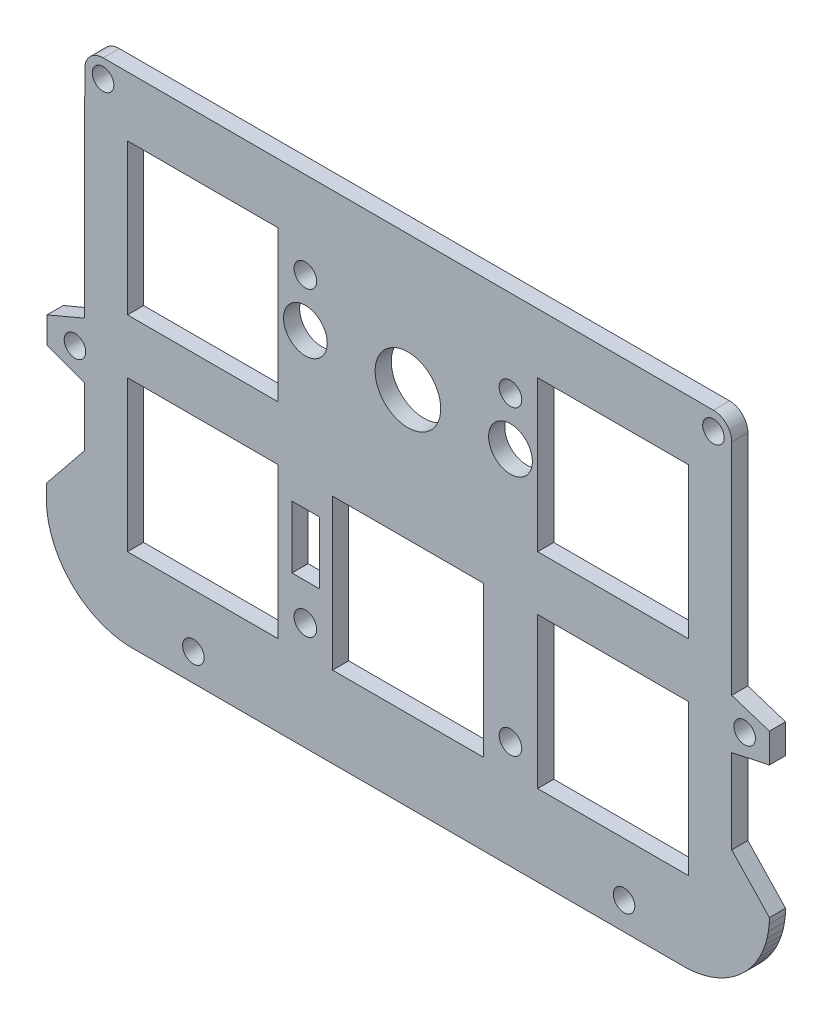
SolidWorks part; units mm, degrees
ref_plane "Front Plane" through (0, 0, 0) normal (0, 0, 1) x (1, 0, 0)
ref_plane "Top Plane" through (0, 0, 0) normal (0, 1, 0) x (1, 0, 0)
ref_plane "Right Plane" through (0, 0, 0) normal (1, 0, 0) x (0, 0, -1)
sketch "Model" plane through (0, 0, 0) normal (0, 0, 1) x (1, 0, 0)
  line L0 (16.6205, 16.7817) -> (2.621, 16.7817)
  line L1 (2.621, 16.7817) -> (2.621, 2.7823)
  line L2 (2.621, 2.7823) -> (16.6205, 2.7823)
  line L3 (16.6205, 2.7823) -> (16.6205, 16.7817)
  line L4 (54.7204, 35.8316) -> (40.7211, 35.8316)
  line L5 (40.7211, 35.8316) -> (40.7211, 21.8323)
  line L6 (40.7211, 21.8323) -> (54.7204, 21.8323)
  line L7 (54.7204, 21.8323) -> (54.7204, 35.8316)
  line L8 (21.671, 16.7817) -> (21.671, 2.7823)
  line L9 (21.671, 2.7823) -> (35.6704, 2.7823)
  line L10 (35.6704, 2.7823) -> (35.6704, 16.7817)
  line L11 (35.6704, 16.7817) -> (21.671, 16.7817)
  line L12 (16.6205, 21.8323) -> (16.6205, 35.8316)
  line L13 (16.6205, 35.8316) -> (2.621, 35.8316)
  line L14 (2.621, 35.8316) -> (2.621, 21.8323)
  line L15 (2.621, 21.8323) -> (16.6205, 21.8323)
  line L16 (40.7211, 16.7817) -> (40.7211, 2.7823)
  line L17 (40.7211, 2.7823) -> (54.7204, 2.7823)
  line L18 (54.7204, 2.7823) -> (54.7204, 16.7817)
  line L19 (54.7204, 16.7817) -> (40.7211, 16.7817)
  line L20 (0.3548, 41.3789) -> (57.0464, 41.3789)
  line L21 (62.2453, 3.1661) -> (62.2262, 2.6367)
  line L22 (62.2262, 2.6367) -> (62.1524, 2.0114)
  line L23 (62.1524, 2.0114) -> (62.0292, 1.3849)
  line L24 (62.0292, 1.3849) -> (61.8553, 0.7766)
  line L25 (61.8553, 0.7766) -> (61.6442, 0.2027)
  line L26 (61.6442, 0.2027) -> (61.3794, -0.3764)
  line L27 (61.3794, -0.3764) -> (61.0647, -0.9348)
  line L28 (61.0647, -0.9348) -> (60.7212, -1.4467)
  line L29 (60.7212, -1.4467) -> (60.333, -1.9414)
  line L30 (60.333, -1.9414) -> (59.9058, -2.4019)
  line L31 (59.9058, -2.4019) -> (59.4459, -2.8288)
  line L32 (59.4459, -2.8288) -> (58.9476, -3.2204)
  line L33 (58.9476, -3.2204) -> (58.4345, -3.5634)
  line L34 (58.4345, -3.5634) -> (57.8802, -3.876)
  line L35 (57.8802, -3.876) -> (57.3021, -4.1405)
  line L36 (57.3021, -4.1405) -> (56.7262, -4.3529)
  line L37 (56.7262, -4.3529) -> (56.116, -4.5268)
  line L38 (56.116, -4.5268) -> (55.4922, -4.6494)
  line L39 (55.4922, -4.6494) -> (54.8784, -4.7221)
  line L40 (54.8784, -4.7221) -> (54.3469, -4.7437)
  line L41 (54.3469, -4.7437) -> (2.9928, -4.7437)
  line L42 (2.9928, -4.7437) -> (2.4645, -4.7221)
  line L43 (2.4645, -4.7221) -> (1.8472, -4.6494)
  line L44 (1.8472, -4.6494) -> (1.2235, -4.5262)
  line L45 (1.2235, -4.5262) -> (0.6156, -4.353)
  line L46 (0.6156, -4.353) -> (0.0383, -4.1402)
  line L47 (0.0383, -4.1402) -> (-0.5328, -3.8785)
  line L48 (-0.5328, -3.8785) -> (-1.0889, -3.5671)
  line L49 (-1.0889, -3.5671) -> (-1.6146, -3.2154)
  line L50 (-1.6146, -3.2154) -> (-2.1023, -2.8297)
  line L51 (-2.1023, -2.8297) -> (-2.5583, -2.4098)
  line L52 (-2.5583, -2.4098) -> (-2.9923, -1.9422)
  line L53 (-2.9923, -1.9422) -> (-3.3906, -1.4349)
  line L54 (-3.3906, -1.4349) -> (-3.7304, -0.9216)
  line L55 (-3.7304, -0.9216) -> (-4.0368, -0.378)
  line L56 (-4.0368, -0.378) -> (-4.2957, 0.1871)
  line L57 (-4.2957, 0.1871) -> (-4.5168, 0.7768)
  line L58 (-4.5168, 0.7768) -> (-4.6871, 1.3875)
  line L59 (-4.6871, 1.3875) -> (-4.8133, 2.0111)
  line L60 (-4.8133, 2.0111) -> (-4.8839, 2.6392)
  line L61 (-4.8839, 2.6392) -> (-4.9049, 3.156)
  line L62 (-4.9049, 3.156) -> (-4.9049, 4.5385)
  line L63 (62.2453, 3.1661) -> (58.7454, 6.8644)
  line L64 (62.2459, 18.1672) -> (62.2456, 15.4347)
  line L65 (58.7464, 39.6789) -> (58.746, 24.9291)
  line L66 (-1.363, 8.918) -> (-1.3598, 14.3941)
  line L67 (-4.9049, 4.5385) -> (-1.363, 8.918)
  line L68 (-4.8537, 15.9201) -> (-4.8535, 18.1008)
  line L69 (-1.3535, 25.2801) -> (-1.3452, 39.6799)
  line L70 (62.2459, 18.1672) -> (58.7458, 19.2969)
  line L71 (58.7458, 19.2969) -> (58.746, 24.9291)
  line L72 (62.2456, 15.4347) -> (58.7457, 14.6854)
  line L73 (-1.3568, 19.58) -> (-1.3535, 25.2801)
  line L74 (-1.358, 14.3935) -> (-4.8537, 15.6658)
  line L75 (-4.8537, 15.9201) -> (-4.8537, 15.6658)
  line L76 (-1.3568, 19.58) -> (-4.8535, 18.1008)
  line L77 (58.7454, 6.8644) -> (58.7457, 14.6854)
  line L78 (17.8976, 8.7136) -> (20.4376, 8.7136)
  line L79 (20.4376, 8.7136) -> (20.4376, 14.4967)
  line L80 (20.4376, 14.4967) -> (17.8976, 14.4967)
  line L81 (17.8976, 14.4967) -> (17.8976, 8.7136)
  circle A0 centre (38.1958, 28.832) radius 2.032
  circle A1 centre (19.1458, 28.832) radius 2.032
  circle A2 centre (28.6708, 28.832) radius 3.048
  circle A3 centre (-2.2555, 16.9102) radius 1
  circle A4 centre (59.9445, 16.9102) radius 1
  circle A5 centre (8.7445, -2.1898) radius 1
  circle A6 centre (48.7445, -2.1898) radius 1
  arc A7 (58.7464, 39.6789) -> (57.0464, 41.3789) centre (57.0464, 39.6789) ccw
  arc A8 (0.3548, 41.3789) -> (-1.3452, 39.6799) centre (0.3548, 39.6789) ccw
  circle A9 centre (57.0464, 39.6789) radius 1
  circle A10 centre (0.3548, 39.6789) radius 1
  circle A11 centre (19.1458, 33.3106) radius 1.05
  circle A12 centre (38.1946, 33.3119) radius 1.05
  circle A13 centre (19.1458, 5.3118) radius 1.05
  circle A14 centre (38.1958, 5.2722) radius 1.05
extrude "凸台-拉伸1" add sketch "Model" along normal blind 1.5
